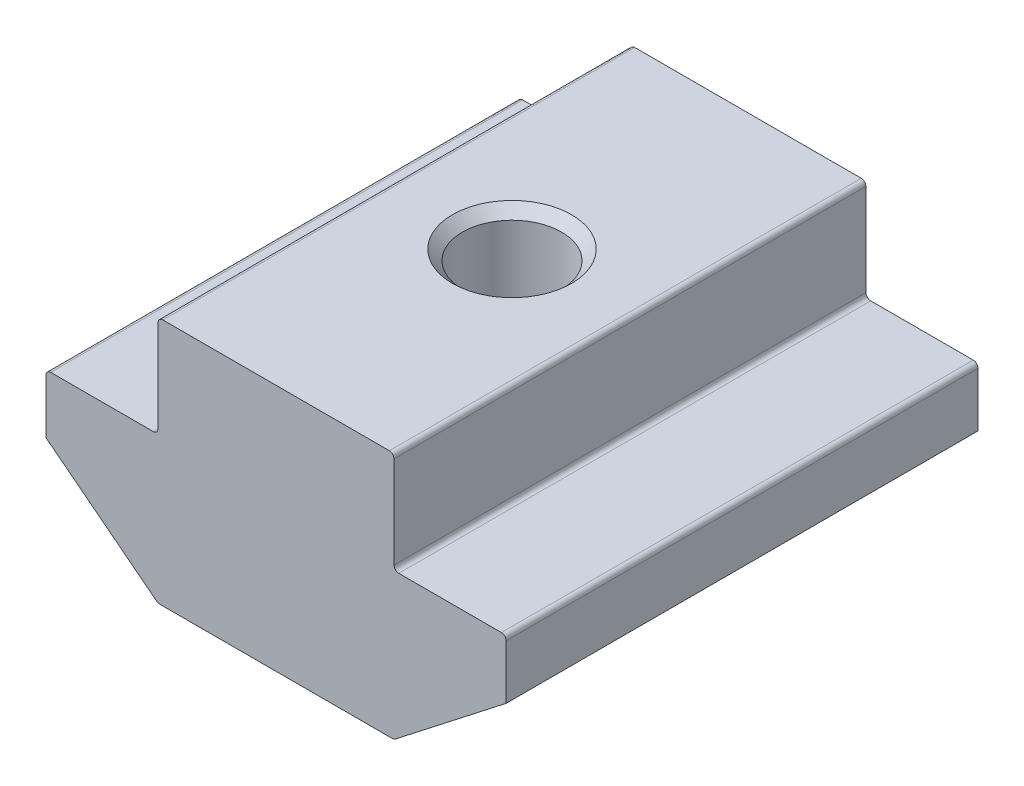
SolidWorks part; units mm, degrees
ref_plane "Спереди" through (0, 0, 0) normal (0, 0, 1) x (1, 0, 0)
ref_plane "Сверху" through (0, 0, 0) normal (0, 1, 0) x (1, 0, 0)
ref_plane "Справа" through (0, 0, 0) normal (1, 0, 0) x (0, 0, -1)
sketch "Эскиз1" plane through (0, 0, 0) normal (0, 0, 1) x (1, 0, 0)
  line L0 (5, 0) -> (-5, 0)
  line L1 (-5, 0) -> (-5, -4.3)
  line L2 (-5, -4.3) -> (-9.75, -4.3)
  line L3 (-9.75, -4.3) -> (-9.75, -6.8)
  line L4 (-9.75, -6.8) -> (-5, -10.5)
  line L5 (-5, -10.5) -> (5, -10.5)
  line L6 (0, -10.5) -> (0, 0) construction
  line L7 (9.75, -6.8) -> (5, -10.5)
  line L8 (9.75, -4.3) -> (9.75, -6.8)
  line L9 (5, -4.3) -> (9.75, -4.3)
  line L10 (5, 0) -> (5, -4.3)
  point P3 (-5, -2.15)
  dimension "D1" = 10
  dimension "D2" = 19.5
  dimension "D3" = 2.5
  dimension "D4" = 10.5
  dimension "D5" = 6.2
extrude "Бобышка-Вытянуть1" add sketch "Эскиз1" along normal mid plane 20
hole_wizard "Отверстие обработанное метчиком M54" positions "Эскиз2" profile "Эскиз4" tap size "M5" standard "ISO" end condition through all
sketch "Эскиз2" plane through (0, 0, 0) normal (0, 1, 0) x (1, 0, 0)
  point P0 (0, 0)
sketch "Эскиз4" plane through (0, 0, 0) normal (1, 0, 0) x (0, 0, 1)
  line L0 (0, 0) -> (0, 10.5)
  line L1 (0, 10.5) -> (2.525, 10.5)
  line L2 (2.1, 10.075) -> (2.1, 0.425)
  line L3 (2.1, 0.425) -> (2.525, 0)
  line L5 (2.525, 0) -> (0, 0)
  line L6 (-2.1, 0.425) -> (-2.525, 0) construction
  line L7 (2.525, 10.5) -> (2.1, 10.075)
  line L8 (-2.525, 10.5) -> (-2.1, 10.075) construction
  line L11 (0, -6.35) -> (0, 107.95) construction
  dimension "Диаметр проходного сверла" = 4.2
  dimension "Глубина проходного сверла" = 10.5
  dimension "Диаметр передней зенковки" = 5.05
  dimension "Угол передней зенковки" = 90
  dimension "Диаметр задней зенковки" = 5.05
  dimension "Угол задней зенковки" = 90
cosmetic thread "Отверстие резьбы1" parameters "D2"=5
fillet "Скругление1" radius 0.2 8 edges at (5, -10.5, 0) (-5, -10.5, 0) (9.75, -4.3, 0) (5, -4.3, 0) (5, 0, 0) (-5, 0, 0) (-9.75, -4.3, 0) (-5, -4.3, 0)
